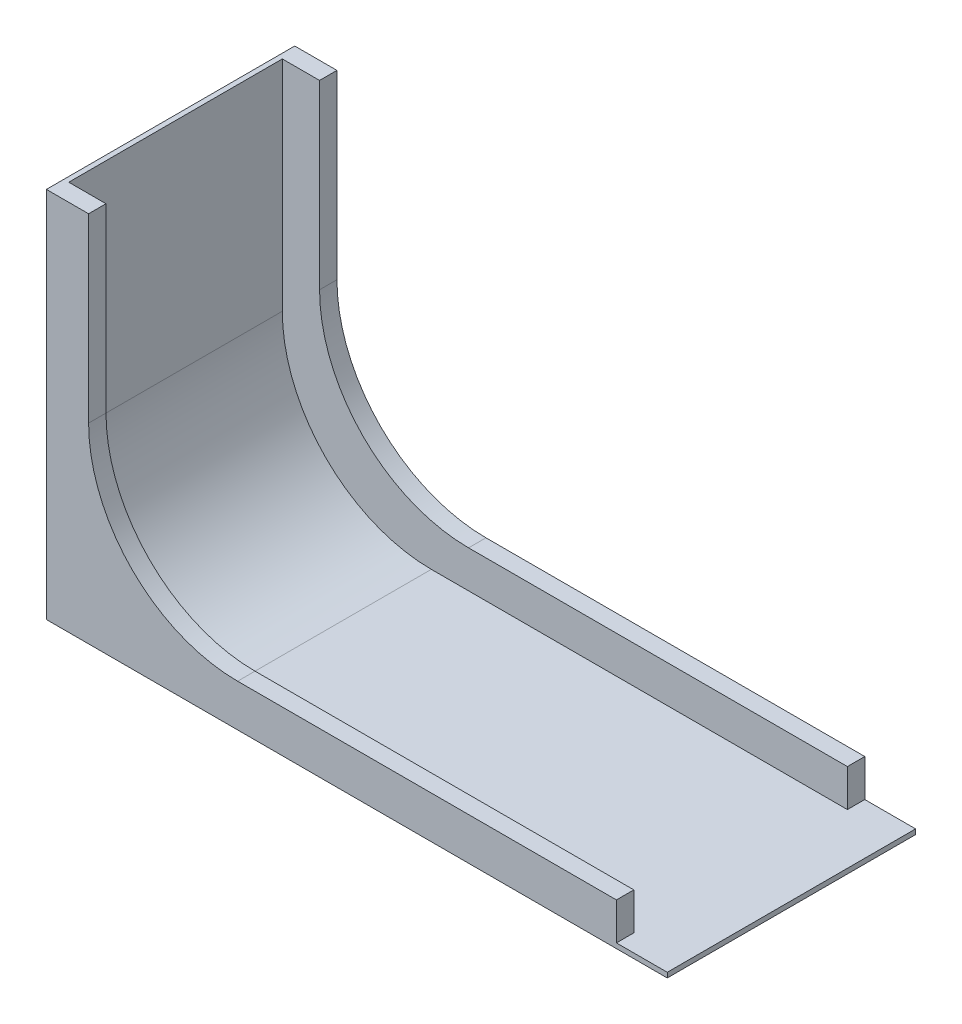
SolidWorks part; units mm, degrees
ref_plane "Front Plane" through (0, 0, 0) normal (0, 0, 1) x (1, 0, 0)
ref_plane "Top Plane" through (0, 0, 0) normal (0, 1, 0) x (1, 0, 0)
ref_plane "Right Plane" through (0, 0, 0) normal (1, 0, 0) x (0, 0, -1)
sketch "Sketch2" plane through (0, 0, 0) normal (0, 0, 1) x (1, 0, 0)
  line L0 (-0.2323, -1.1037) -> (-50.2323, -1.1037)
  line L1 (-0.2323, 0.8963) -> (199.7677, 0.8963)
  line L3 (-0.2323, -1.1037) -> (199.7677, -1.1037)
  line L4 (199.7677, 0.8963) -> (199.7677, -1.1037)
  line L5 (-50.2323, -1.1037) -> (-50.2323, 148.8963)
  line L6 (-50.2323, 148.8963) -> (-48.2323, 148.8963)
  line L7 (-48.2323, 148.8963) -> (-48.2323, 0.8963)
  line L8 (-48.2323, 0.8963) -> (-3.2937, 0.8963)
  line L9 (-3.2937, 0.8963) -> (-0.2323, 0.8963)
  dimension "D1" = 2
  dimension "D2" = 200
  dimension "D3" = 50
  dimension "D4" = 150
extrude "Boss-Extrude1" add sketch "Sketch2" along normal blind 100
sketch "Sketch5" plane through (0, 0.8963, 0) normal (0, 1, 0) x (1, 0, 0)
  line L0 (-48.2323, -100) -> (-48.2323, 0) construction
  line L1 (199.7677, -100) -> (-48.2323, -100)
  line L2 (199.7677, -100) -> (199.7677, -93)
  line L3 (199.7677, -93) -> (-48.2323, -93)
  line L4 (-48.2323, -100) -> (-48.2323, -93)
  line L5 (-48.2323, -100) -> (-48.2323, 0) construction
  line L6 (199.7677, 0) -> (-48.2323, 0)
  line L7 (199.7677, 0) -> (199.7677, -7)
  line L8 (199.7677, -7) -> (-48.2323, -7)
  line L9 (-48.2323, 0) -> (-48.2323, -7)
  line L11 (199.7677, 0) -> (179.2942, 0)
  line L12 (199.7677, 0) -> (199.7677, -7)
  line L13 (199.7677, -7) -> (179.2942, -7)
  line L14 (179.2942, 0) -> (179.2942, -7)
  line L15 (199.7677, -93) -> (179.2942, -93)
  line L16 (199.7677, -93) -> (199.7677, -100)
  line L17 (199.7677, -100) -> (179.2942, -100)
  line L18 (179.2942, -93) -> (179.2942, -100)
  line M4 (-48.2323, 0) -> (-48.2323, -100)
  line M5 (-48.2323, -100) -> (199.7677, -100)
  dimension "D1" = 7
  dimension "D2" = 7
extrude "Boss-Extrude4" add sketch "Sketch5" along normal blind 15 contours L14 L6 L8 M4 | L18 L3 M4 M5
sketch "Sketch6" plane through (-48.2323, 0, 0) normal (1, 0, 0) x (0, 0, -1)
  line L1 (-100, 148.8963) -> (-93, 148.8963)
  line L2 (-100, 148.8963) -> (-100, 15.8963)
  line L3 (-100, 15.8963) -> (-93, 15.8963)
  line L4 (-93, 148.8963) -> (-93, 15.8963)
  line L5 (0, 148.8963) -> (-7, 148.8963)
  line L6 (0, 148.8963) -> (0, 15.8963)
  line L7 (0, 15.8963) -> (-7, 15.8963)
  line L8 (-7, 148.8963) -> (-7, 15.8963)
extrude "Boss-Extrude5" add sketch "Sketch6" along normal blind 15
fillet "Fillet2" radius 60 3 edges at (-33.2323, 15.8963, 96.5) (-33.2323, 15.8963, 3.5) (-48.2323, 0.8963, 50)
